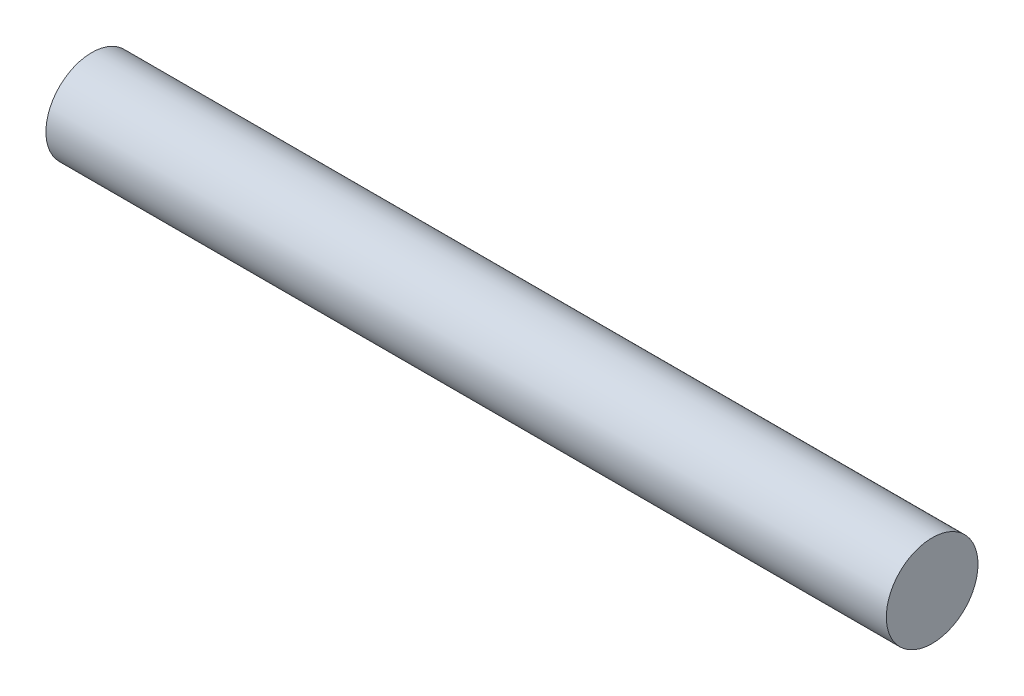
SolidWorks part; units mm, degrees
ref_plane "Front Plane" through (0, 0, 0) normal (0, 0, 1) x (1, 0, 0)
ref_plane "Top Plane" through (0, 0, 0) normal (0, 1, 0) x (1, 0, 0)
ref_plane "Right Plane" through (0, 0, 0) normal (1, 0, 0) x (0, 0, -1)
sketch "Sketch2" plane through (0, 0, 0) normal (1, 0, 0) x (0, 0, -1)
  circle A0 centre (0, 0) radius 0.6
  dimension "D1" = 1.2
extrude "Boss-Extrude1" add sketch "Sketch2" along normal blind 11
